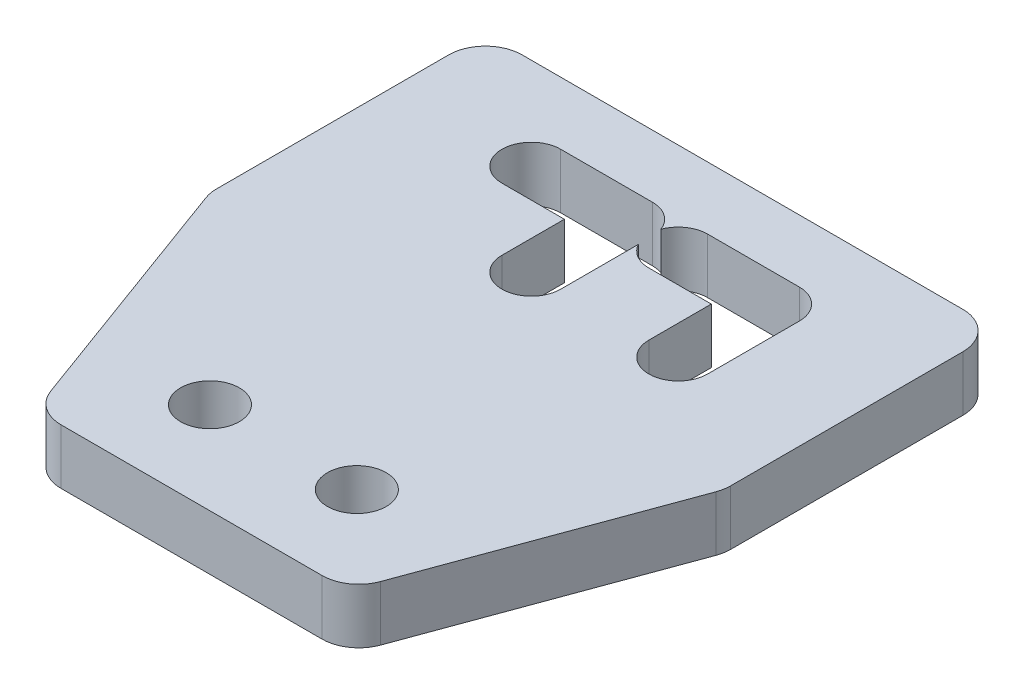
SolidWorks part; units mm, degrees
material "Beech"
ref_plane "Front Plane" through (0, 0, 0) normal (0, 0, 1) x (1, 0, 0)
ref_plane "Top Plane" through (0, 0, 0) normal (0, 1, 0) x (1, 0, 0)
ref_plane "Right Plane" through (0, 0, 0) normal (1, 0, 0) x (0, 0, -1)
sketch "Sketch1" plane through (0, 0, 0) normal (0, 1, 0) x (1, 0, 0)
  line L0 (6.5, 15) -> (6.5, 10) construction
  line L1 (-14, -15) -> (14, -15)
  line L2 (-14, -15) -> (-14, 15)
  line L3 (-14, 15) -> (14, 15)
  line L4 (14, -15) -> (14, 15)
  line L5 (-14, -15) -> (14, 15) construction
  line L6 (-14, 15) -> (14, -15) construction
  line L7 (6.5, 10) -> (-1.5, 10) construction
  line L8 (6.5, 10) -> (2.4061, 5.6137) construction
  line L9 (7.6697, 8.9083) -> (3.5758, 4.522) construction
  line L10 (5.3303, 11.0917) -> (1.2364, 6.7054) construction
  line L11 (-1.5, 10) -> (-5.5939, 5.6137) construction
  line L12 (-0.3303, 8.9083) -> (-4.4242, 4.522) construction
  line L13 (-2.6697, 11.0917) -> (-6.7636, 6.7054) construction
  line L14 (-1.5, 10) -> (-1.5, 5) construction
  line L15 (0.1, 10) -> (0.1, 5)
  line L16 (-3.1, 10) -> (-3.1, 5)
  line L17 (6.5, 10) -> (6.5, 5) construction
  line L18 (8.1, 10) -> (8.1, 5)
  line L19 (4.9, 10) -> (4.9, 5)
  line L20 (6.5, 10) -> (1.5, 10) construction
  line L21 (6.5, 8.4) -> (1.5, 8.4)
  line L22 (6.5, 11.6) -> (1.5, 11.6)
  line L23 (-1.5, 10) -> (-6.5, 10) construction
  line L24 (-1.5, 8.4) -> (-6.5, 8.4)
  line L25 (-1.5, 11.6) -> (-6.5, 11.6)
  line L26 (6.5, 10) -> (14, 10) construction
  line L27 (-6.5, 10) -> (-14, 10) construction
  circle A0 centre (6.5, 10) radius 1.6 construction
  circle A1 centre (-1.5, 10) radius 1.6 construction
  arc A2 (7.6697, 8.9083) -> (5.3303, 11.0917) centre (6.5, 10) ccw construction
  arc A3 (1.2364, 6.7054) -> (3.5758, 4.522) centre (2.4061, 5.6137) ccw construction
  arc A4 (-0.3303, 8.9083) -> (-2.6697, 11.0917) centre (-1.5, 10) ccw construction
  arc A5 (-6.7636, 6.7054) -> (-4.4242, 4.522) centre (-5.5939, 5.6137) ccw construction
  arc A6 (0.1, 10) -> (-3.1, 10) centre (-1.5, 10) ccw
  arc A7 (-3.1, 5) -> (0.1, 5) centre (-1.5, 5) ccw
  arc A8 (8.1, 10) -> (4.9, 10) centre (6.5, 10) ccw
  arc A9 (4.9, 5) -> (8.1, 5) centre (6.5, 5) ccw
  arc A10 (6.5, 8.4) -> (6.5, 11.6) centre (6.5, 10) ccw
  arc A11 (1.5, 11.6) -> (1.5, 8.4) centre (1.5, 10) ccw
  arc A12 (-1.5, 8.4) -> (-1.5, 11.6) centre (-1.5, 10) ccw
  arc A13 (-6.5, 11.6) -> (-6.5, 8.4) centre (-6.5, 10) ccw
  point P0 (0, 0)
  point P11 (4.453, 7.8068)
  point P17 (-3.547, 7.8068)
  point P25 (-1.5, 7.5)
  point P30 (6.5, 7.5)
  point P39 (4, 10)
  point P44 (-4, 10)
  dimension "D5" = 3.2
  dimension "D6" = 6
  dimension "D8" = 8
  dimension "D10" = 5
  dimension "D1" = 28
  dimension "D2" = 30
  dimension "D3" = 5
  dimension "D7" = 6
  dimension "D9" = 5
  dimension "D11" = 5
extrude "Boss-Extrude1" add sketch "Sketch1" along normal blind 3 contours L1 L4 L3 L2 A13 L25 A6 A11 L22 A2 L18 A9 L19 L9 A3 L10 L21 L15 A7 L16 L12 A5 L13 L24
sketch "Sketch2" plane through (0, 3, 0) normal (0, 1, 0) x (1, 0, 0)
  line L0 (-4, -15) -> (-4, -10) construction
  line L1 (-14, -15) -> (14, -15) construction
  line L2 (0, -15) -> (0, 0) construction
  line L3 (14, 0) -> (8.5, -15)
  line L4 (14, -15) -> (14, 15) construction
  line L5 (8.5, -15) -> (14, -15)
  line L6 (14, -15) -> (14, 0)
  line L7 (-8.5, -15) -> (-14, -15)
  line L8 (-14, -15) -> (-14, 0)
  line L9 (-14, 0) -> (-8.5, -15)
  circle A0 centre (-4, -10) radius 1.6
  circle A1 centre (4, -10) radius 1.6
  point P4 (0, -15)
  dimension "D3" = 3.2
  dimension "D1" = 4
  dimension "D2" = 5
  dimension "D4" = 5.5
extrude "Cut-Extrude1" cut sketch "Sketch2" against normal through all
fillet "Fillet1" radius 2 6 edges at (14, 1.5, -15) (14, 1.5, 0) (8.5, 1.5, 15) (-8.5, 1.5, 15) (-14, 1.5, 0) (-14, 1.5, -15)
